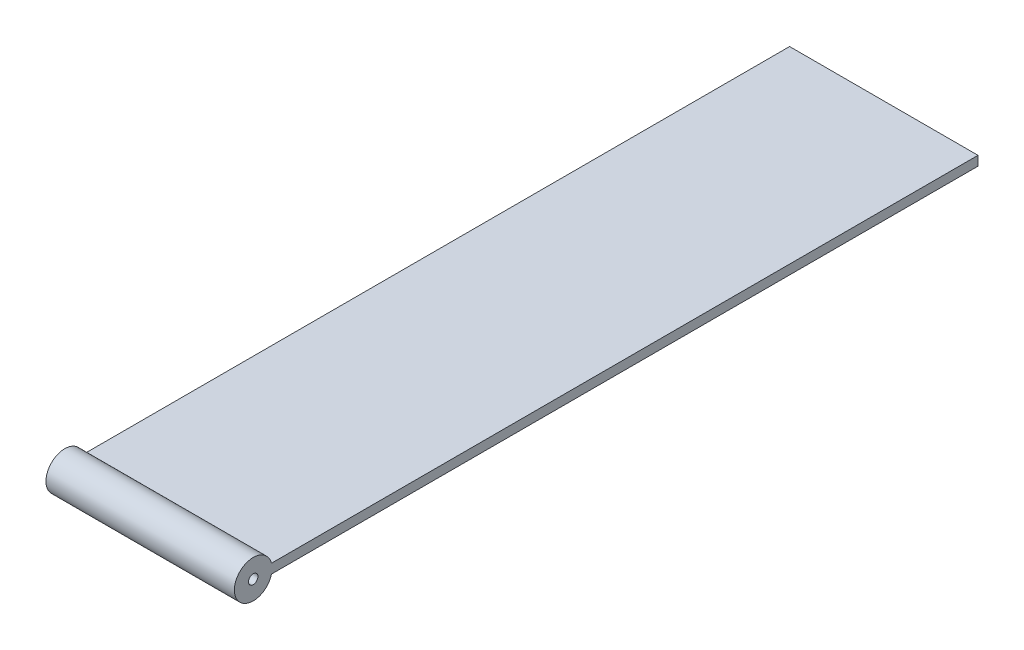
SolidWorks part; units mm, degrees
ref_plane "Front Plane" through (0, 0, 0) normal (0, 0, 1) x (1, 0, 0)
ref_plane "Top Plane" through (0, 0, 0) normal (0, 1, 0) x (1, 0, 0)
ref_plane "Right Plane" through (0, 0, 0) normal (1, 0, 0) x (0, 0, -1)
sketch "Sketch1" plane through (0, 0, 0) normal (1, 0, 0) x (0, 0, -1)
  line L0 (-18.9724, 1) -> (131.0276, 1)
  line L1 (-18.9724, -1) -> (131.0276, -1)
  line L2 (131.0276, 1) -> (131.0276, -1)
  circle A0 centre (-22.8453, 0) radius 1
  circle A1 centre (-22.8453, 0) radius 4
  point P5 (0, 0)
  dimension "D1" = 2
  dimension "D2" = 8
  dimension "D3" = 150
extrude "Boss-Extrude1" add sketch "Sketch1" along normal blind 20 and the other way blind 20 contours A1 A0 | A1 L1 L2 L0
